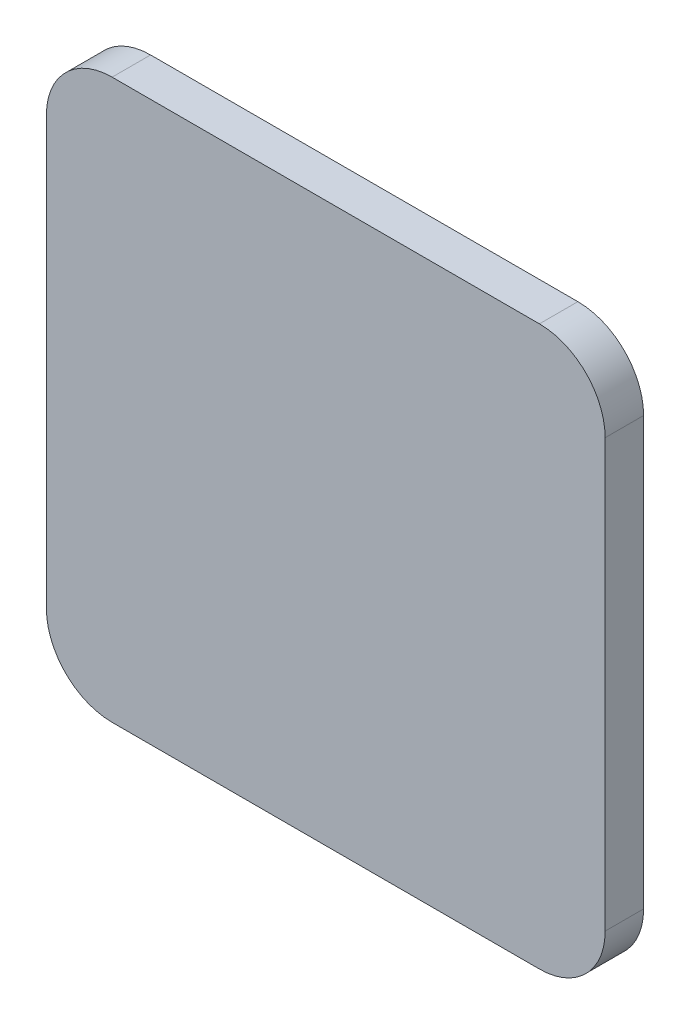
SolidWorks part; units mm, degrees
ref_plane "Front Plane" through (0, 0, 0) normal (0, 0, 1) x (1, 0, 0)
ref_plane "Top Plane" through (0, 0, 0) normal (0, 1, 0) x (1, 0, 0)
ref_plane "Right Plane" through (0, 0, 0) normal (1, 0, 0) x (0, 0, -1)
sketch "Sketch1" plane through (0, 0, 0) normal (0, 0, 1) x (1, 0, 0)
  line L1 (-50.2183, -95.1961) -> (14.7817, -95.1961)
  line L2 (-60.2183, -85.1961) -> (-60.2183, -20.1961)
  line L3 (-50.2183, -10.1961) -> (14.7817, -10.1961)
  line L4 (24.7817, -85.1961) -> (24.7817, -20.1961)
  line L5 (-60.2183, -95.1961) -> (24.7817, -10.1961) construction
  line L6 (-60.2183, -10.1961) -> (24.7817, -95.1961) construction
  arc A0 (14.7817, -95.1961) -> (24.7817, -85.1961) centre (14.7817, -85.1961) ccw
  arc A1 (14.7817, -10.1961) -> (24.7817, -20.1961) centre (14.7817, -20.1961) cw
  arc A2 (-60.2183, -20.1961) -> (-50.2183, -10.1961) centre (-50.2183, -20.1961) cw
  arc A3 (-50.2183, -95.1961) -> (-60.2183, -85.1961) centre (-50.2183, -85.1961) cw
  point P0 (-17.7183, -52.6961)
  dimension "D3" = 10
  dimension "D1" = 85
  dimension "D2" = 85
extrude "Boss-Extrude1" add sketch "Sketch1" along normal offset from surface (5.85 mm away) 0.3 contours L4 A1 L3 A2 L2 A3 L1 A0
